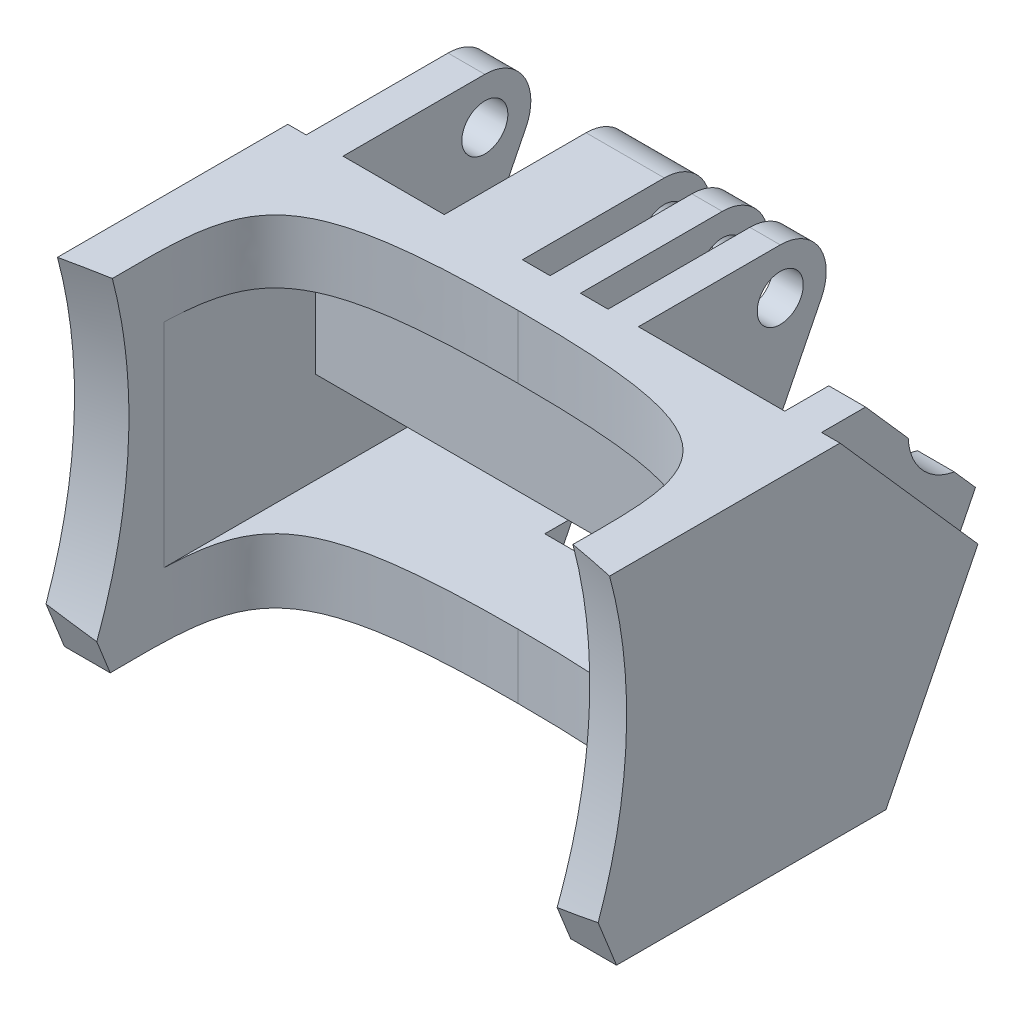
SolidWorks part; units mm, degrees
ref_plane "Front Plane" through (0, 0, 0) normal (0, 0, 1) x (1, 0, 0)
ref_plane "Top Plane" through (0, 0, 0) normal (0, 1, 0) x (1, 0, 0)
ref_plane "Right Plane" through (0, 0, 0) normal (1, 0, 0) x (0, 0, -1)
sketch "Sketch1" plane through (0, 0, 0) normal (0, 1, 0) x (1, 0, 0)
  line L0 (0, -78.885) -> (0, 78.885) construction
  line L3 (-30, -13.4266) -> (-25, -13.4266)
  line L5 (-25, -0.7182) -> (-25, -26.135) construction
  line L6 (13.8627, 9.5734) -> (-13.8627, 9.5734) construction
  line L12 (-30, 29.5734) -> (30, 29.5734)
  line L16 (-30, -13.4266) -> (-30, 29.5734)
  line L17 (30, -13.4266) -> (30, 29.5734)
  line L18 (30, -13.4266) -> (25, -13.4266)
  spline S0 degree 3 poles (-25, -13.4266) (-25, 4.4304) (-27.18, 9.5734) (0, 9.5734) knots 0 0 0 0 1 1 1 1
  spline S1 degree 3 poles (25, -13.4266) (25, 4.4304) (27.18, 9.5734) (0, 9.5734) knots 0 0 0 0 1 1 1 1
  point P1 (0, 29.5734)
  point P8 (0, 0)
  point P11 (0, 29.5734)
  point P17 (0, 14.5734)
  dimension "D1" = 43
  dimension "D3" = 5
  dimension "D4" = 5
extrude "Boss-Extrude1" add sketch "Sketch1" along normal blind 37
sketch "Sketch3" plane through (30, 0, 0) normal (1, 0, 0) x (0, 0, -1)
  line L0 (14.5734, 37) -> (29.5734, 20)
  line L5 (29.5734, 20) -> (19.5734, 0)
  line L7 (-13.4266, 37) -> (29.5734, 37) construction
  line L8 (29.5734, 37) -> (29.5734, 0) construction
  line L9 (-13.4266, 0) -> (29.5734, 0) construction
  point P2 (17.5734, 37)
  point P4 (29.5734, 20)
  point P6 (17.5734, 32)
  point P8 (19.5734, 0)
  point P11 (27.5734, 20)
  point P13 (17.9469, 36.3651)
  dimension "D1" = 10
  dimension "D2" = 20
  dimension "D3" = 15
extrude "Cut-Extrude1" cut sketch "Sketch3" against normal through all and the other way through all
sketch "Sketch4" plane through (0, 23.4265, -26.55) normal (0, 0.6616, -0.7498) x (-1, 0, 0)
  line L0 (-24, 18.1019) -> (-24, -4.5697)
  line L5 (-8.1, 18.1019) -> (-4.8, 18.1019)
  line L7 (-28, 18.1019) -> (-24, 18.1019)
  line L9 (-28, -4.5697) -> (-24, -4.5697)
  line L12 (-28, 18.1019) -> (-28, -4.5697)
  line L13 (-8.1, 18.1019) -> (-8.1, -4.5697)
  line L14 (-8.1, -4.5697) -> (-4.8, -4.5697)
  line L15 (-4.8, 18.1019) -> (-4.8, -4.5697)
  line L16 (-1.8, 18.1019) -> (1.5, 18.1019)
  line L17 (-1.8, 18.1019) -> (-1.8, -4.5697)
  line L18 (-1.8, -4.5697) -> (1.5, -4.5697)
  line L19 (1.5, 18.1019) -> (1.5, -4.5697)
  line L20 (4.5, 18.1019) -> (13, 18.1019)
  line L21 (4.5, 18.1019) -> (4.5, -4.5697)
  line L22 (4.5, -4.5697) -> (13, -4.5697)
  line L23 (13, 18.1019) -> (13, -4.5697)
  line L24 (24, 18.1019) -> (28, 18.1019)
  line L25 (24, 18.1019) -> (24, -4.5697)
  line L26 (24, -4.5697) -> (28, -4.5697)
  line L27 (28, 18.1019) -> (28, -4.5697)
  line L28 (-8.1, 18.1019) -> (-4.8, 18.1019)
  line L29 (-8.1, -4.5697) -> (-4.8, -4.5697)
  line L30 (-1.8, 18.1019) -> (1.5, 18.1019)
  line L31 (-1.8, -4.5697) -> (1.5, -4.5697)
  line L32 (4.5, -4.5697) -> (13, -4.5697)
  line L33 (24, 18.1019) -> (28, 18.1019)
  line L34 (24, -4.5697) -> (28, -4.5697)
  line L35 (4.5, 18.1019) -> (13, 18.1019)
  line L36 (-30, -4.5697) -> (30, -4.5697) construction
  line L37 (30, 18.1019) -> (-30, 18.1019) construction
  line L38 (30, -4.5697) -> (30, 18.1019) construction
  line M5 (-30, -4.5697) -> (30, -4.5697)
  line M7 (30, 18.1019) -> (-30, 18.1019)
  dimension "D1" = 4
  dimension "D2" = 3.3
  dimension "D3" = 3.3
  dimension "D4" = 8.5
  dimension "D5" = 3
  dimension "D6" = 3
  dimension "D7" = 4
  dimension "D8" = 0
  dimension "D9" = 0
  dimension "D10" = 17
extrude "Boss-Extrude2" add sketch "Sketch4" along normal blind 22 contours L12 L0 M7 M5 | L15 L13 M7 M5 | L19 L17 M7 M5 | L23 L21 M7 M5 | L27 L25 M7 M5
sketch "Sketch5" plane through (-30, 0, 0) normal (-1, 0, 0) x (0, 0, 1)
  line L9 (-29.5734, 20) -> (-14.5734, 37) construction
  line L10 (-29.5734, 20) -> (-34.4554, 29.7639)
  line L12 (-19.5734, 0) -> (-29.5734, 20) construction
  line L13 (-14.5734, 37) -> (-29.9833, 37)
  line L14 (-14.5734, 37) -> (13.4266, 37) construction
  line L15 (-46.0699, 34.5557) -> (-29.5734, 20)
  line L16 (-46.0699, 34.5557) -> (-31.0699, 51.5557)
  line L17 (-31.0699, 51.5557) -> (-14.5734, 37)
  arc A2 (-34.4554, 29.7639) -> (-29.9833, 37) centre (-29.9833, 32) cw
  circle A3 centre (-29.9833, 32) radius 2.5
  point P5 (-28.7293, 20.9567)
  point P10 (-17.8889, 32.2629)
  dimension "D1" = 180
  dimension "D2" = 180
  dimension "D3" = 5
  dimension "D4" = 5
  dimension "D5" = 5
  dimension "D6" = 5
extrude "Cut-Extrude3" cut sketch "Sketch5" against normal through all
sketch "Sketch6" plane through (28, 0, 0) normal (1, 0, 0) x (0, 0, -1)
  line L0 (19.3577, 37) -> (23.9884, 31.7519)
  line L4 (29.9833, 37) -> (14.5734, 37) construction
  line L5 (29.5734, 20) -> (34.4554, 29.7639) construction
  line L6 (14.5734, 37) -> (29.5734, 20) construction
  line L7 (28.9906, 26.0827) -> (31.3039, 23.461)
  line L8 (19.3577, 37) -> (39.3425, 37)
  line L9 (31.3039, 23.461) -> (39.3425, 37)
  arc A0 (23.9884, 31.7519) -> (28.9906, 26.0827) centre (29.9833, 32) ccw
  dimension "D1" = 12
extrude "Cut-Extrude4" cut sketch "Sketch6" against normal blind 5
sketch "Sketch8" plane through (-30, 0, 0) normal (-1, 0, 0) x (0, 0, 1)
  line L0 (-19.5734, 0) -> (13.4266, 0) construction
  line L1 (-37.174, 17) -> (-24.1435, 17)
  line L2 (-37.174, 17) -> (-37.174, 7)
  line L3 (-37.174, 7) -> (24.041, 7)
  line L4 (24.041, 17) -> (24.041, 7)
  line L6 (-12.5593, 30.1288) -> (16.916, 30.1288)
  line L8 (16.916, 30.1288) -> (24.041, 17)
  line L9 (-12.5593, 30.1288) -> (-12.5593, 17)
  line L10 (-12.5593, 17) -> (-24.1435, 17)
  dimension "D1" = 3
  dimension "D2" = 7
extrude "Cut-Extrude5" cut sketch "Sketch8" against normal blind 50 from offset 5 offset against normal yes
sketch "Sketch9" plane through (-13, 0, 0) normal (-1, 0, 0) x (0, 0, 1)
  line L1 (-28.681, 27.5987) -> (-25.5205, 30.9271)
  line L2 (-25.5205, 30.9271) -> (-26.8227, 35.3284)
  line L3 (-26.8227, 35.3284) -> (-31.2855, 36.4013)
  line L4 (-31.2855, 36.4013) -> (-34.446, 33.0729)
  line L5 (-34.446, 33.0729) -> (-33.1438, 28.6716)
  line L6 (-33.1438, 28.6716) -> (-28.681, 27.5987)
  circle A0 centre (-29.9833, 32) radius 3.975 construction
  dimension "D1" = 7.95
extrude "Cut-Extrude6" cut sketch "Sketch9" against normal blind 5
ref_plane "Plane1" through (0, 23, 0) normal (0, 1, 0) x (1, 0, 0)
sketch "Sketch11" plane through (0, 23, 0) normal (0, 1, 0) x (1, 0, 0)
  line L0 (0, 0) -> (0, -103.4751) construction
  line L1 (-30, -3.7818) -> (-30, -167.845) construction
  line L2 (-30, 14.5734) -> (-30, -13.4266) construction
  line L3 (30, 0) -> (30, -194.3626) construction
  line L4 (30, -13.4266) -> (30, 14.5734) construction
  line L5 (-30, -62.4936) -> (30, -62.4936) construction
  line L6 (-50.032, -14.3334) -> (49.362, -14.0909)
  arc A0 (49.362, -14.0909) -> (-50.032, -14.3334) centre (0, -151.4932) ccw
  point P16 (-30, -92.8388)
  point P17 (30, -92.5903)
  point P18 (-0.3563, -5.4936)
  point P19 (0, 0)
  point P20 (0, 0)
  point P21 (0, -143.6372)
  point P22 (0, -153.0407)
  point P23 (0, -201.2991)
  point P24 (0, -199.2628)
  point P25 (0, -187.0653)
  point P26 (0, -151.7727)
  point P27 (0, -152.365)
  point P28 (0, -148.0343)
  point P29 (0, -151.4932)
  dimension "D1" = 292
  dimension "D2" = 57
revolve "Cut-Revolve1" cut sketch "Sketch11" angle 360 about L5
sketch "Sketch12" plane through (30, 0, 0) normal (1, 0, 0) x (0, 0, -1)
  line L0 (-11.7039, 5) -> (-9.7039, 0)
  line L1 (-9.7039, 0) -> (-17.4257, 0)
  line L2 (-17.4257, 0) -> (-11.7039, 5)
  line L3 (-13.4266, 0) -> (19.5734, 0) construction
  arc A0 (-13.4266, 0.7285) -> (-10.459, 37) centre (-62.4936, 23) ccw construction
  point P2 (-12.0303, 2.62)
  point P7 (-10.8166, 0)
  point P10 (-17.4257, 0)
  dimension "D1" = 5
  dimension "D2" = 2
extrude "Cut-Extrude7" cut sketch "Sketch12" against normal through all
ref_plane "Plane2" through (0, 0, -28) normal (0, 0, 1) x (1, 0, 0)
sketch "Sketch13" plane through (0, 0, -28) normal (0, 0, 1) x (1, 0, 0)
  line L0 (25, 7) -> (-25, 7) construction
  line L1 (7.5, 7) -> (-7.5, 7)
  line L2 (7.5, 7) -> (7.5, 0)
  line L3 (7.5, 0) -> (-7.5, 0)
  line L4 (-7.5, 7) -> (-7.5, 0)
  line L5 (-30, 0) -> (30, 0) construction
  point P4 (0, 0)
  dimension "D1" = 0
  dimension "D2" = 15
  dimension "D3" = 0
  dimension "D4" = 0
extrude "Cut-Extrude8" cut sketch "Sketch13" along normal blind 8
ref_plane "Plane3" through (0, 0, -30) normal (0, 0, 1) x (1, 0, 0)
sketch "Sketch14" plane through (0, 0, -30) normal (0, 0, 1) x (1, 0, 0)
  line L0 (-25, 17) -> (25, 17) construction
  line L1 (7.5, 20) -> (-7.5, 20)
  line L2 (7.5, 20) -> (7.5, 17)
  line L3 (7.5, 17) -> (-7.5, 17)
  line L4 (-7.5, 20) -> (-7.5, 17)
  line L5 (7.5, 20) -> (-7.5, 17) construction
  line L6 (7.5, 17) -> (-7.5, 20) construction
  line L7 (7.5, 0.8531) -> (7.5, 7) construction
  point P0 (0, 18.5)
  dimension "D1" = 3
  dimension "D2" = 0
  dimension "D3" = 15
  dimension "D4" = 0
extrude "Cut-Extrude9" cut sketch "Sketch14" along normal blind 13
